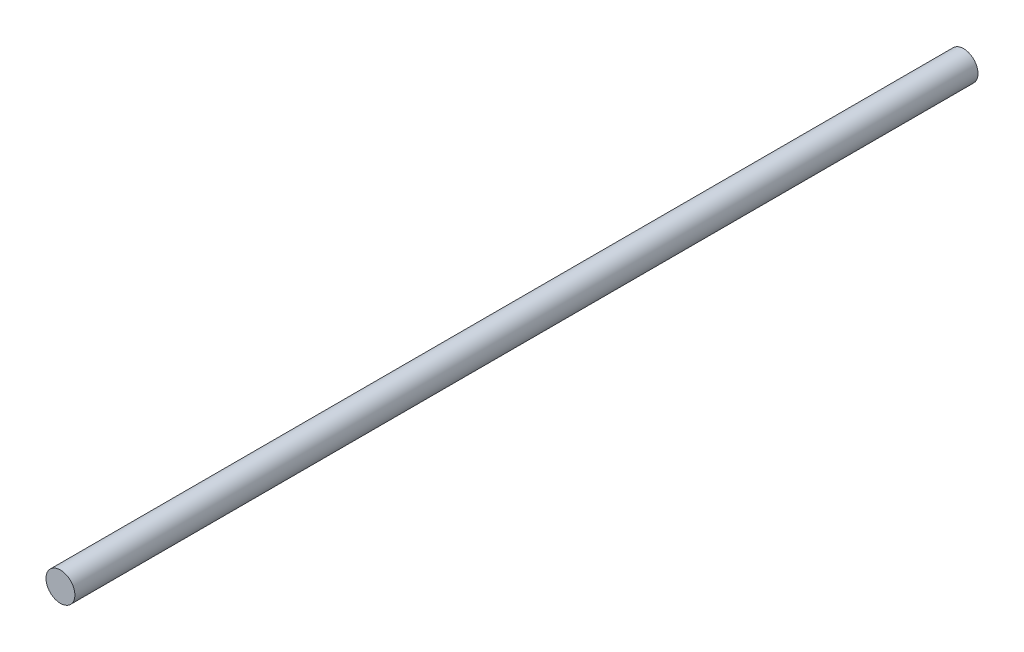
SolidWorks part; units mm, degrees
material "Nickel"
ref_plane "Front Plane" through (0, 0, 0) normal (0, 0, 1) x (1, 0, 0)
ref_plane "Top Plane" through (0, 0, 0) normal (0, 1, 0) x (1, 0, 0)
ref_plane "Right Plane" through (0, 0, 0) normal (1, 0, 0) x (0, 0, -1)
sketch "Sketch1" plane through (0, 0, 0) normal (0, 0, 1) x (1, 0, 0)
  circle A0 centre (0, 0) radius 1.016
  dimension "D1" = 2.032
extrude "Boss-Extrude1" add sketch "Sketch1" against normal blind 63.5 contours A0
